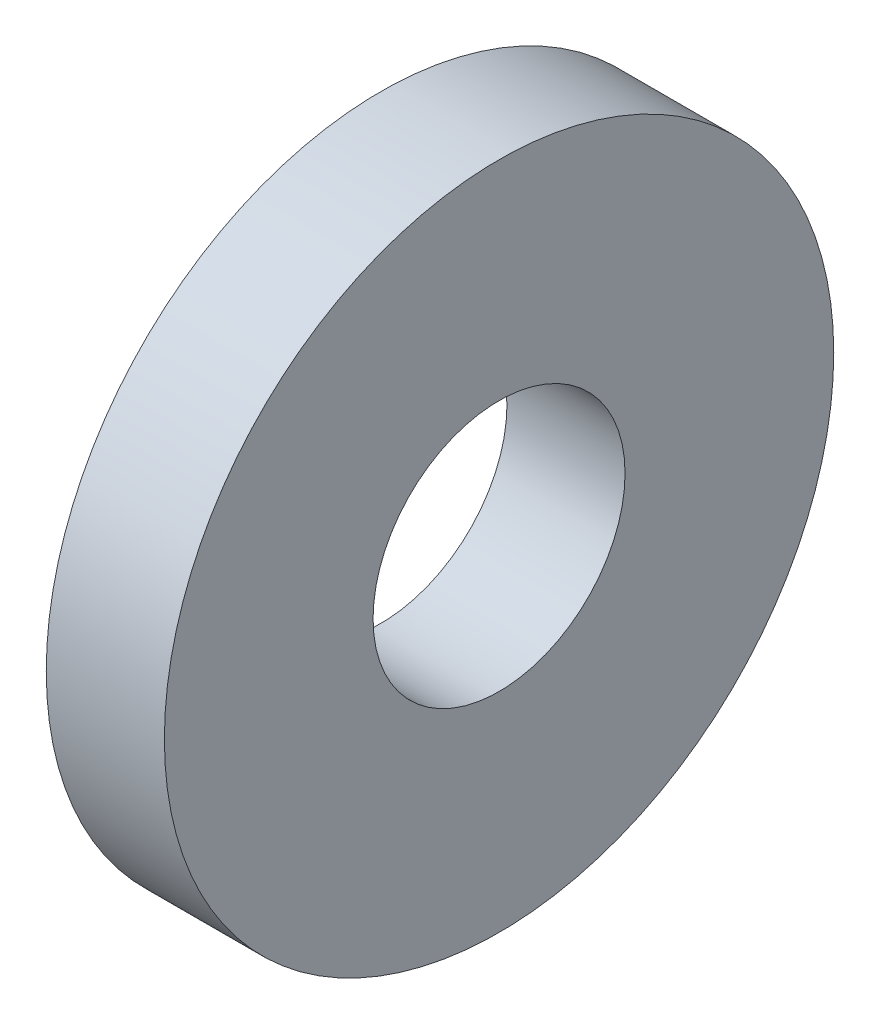
SolidWorks part; units mm, degrees
ref_plane "Plane1" through (0, 0, 0) normal (0, 0, 1) x (1, 0, 0)
ref_plane "Plane2" through (0, 0, 0) normal (0, 1, 0) x (1, 0, 0)
ref_plane "Plane3" through (0, 0, 0) normal (1, 0, 0) x (0, 0, -1)
sketch "Sketch1" plane through (0, 0, 0) normal (1, 0, 0) x (0, 0, -1)
  circle A0 centre (0.5737, -0.8606) radius 8.5
  circle A1 centre (0.5737, -0.8606) radius 3.2
  dimension "OutsideDia" = 17
  dimension "Insid_Dia" = 6.4
extrude "Base-Extrude" add sketch "Sketch1" along normal blind 3
